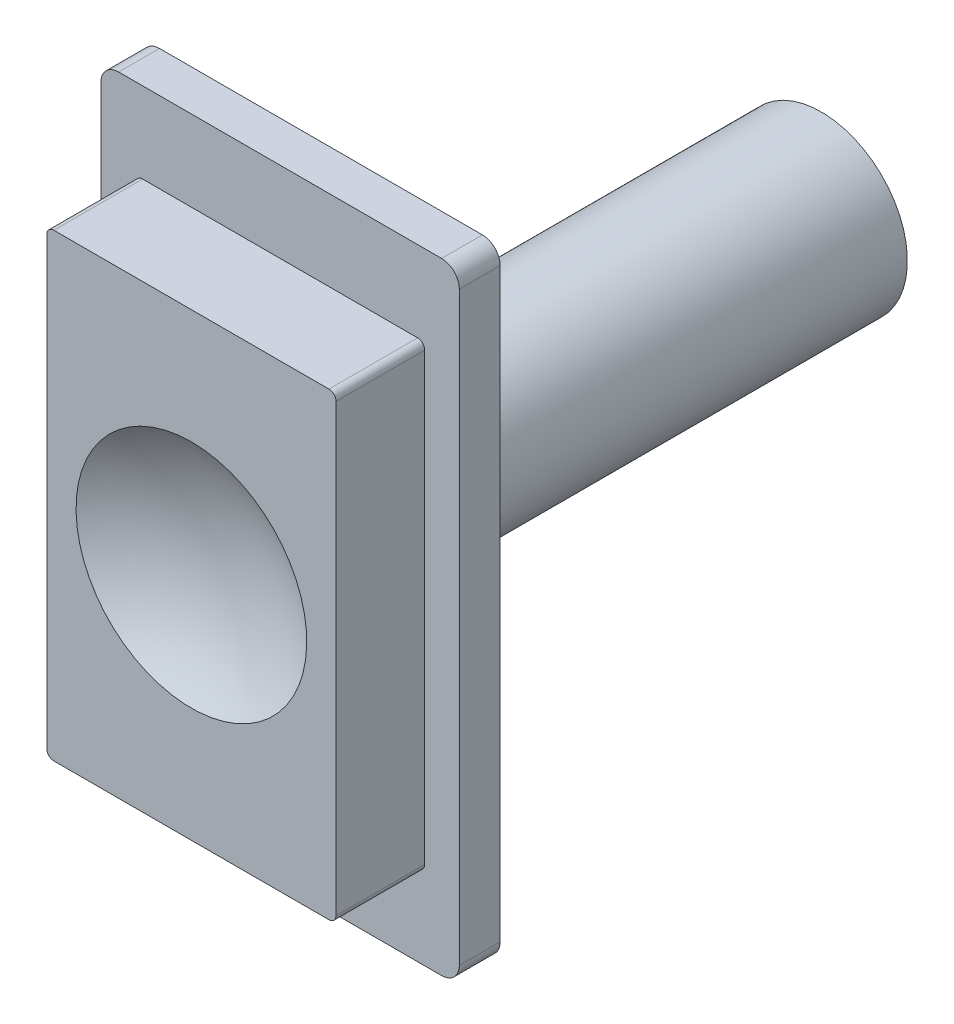
SolidWorks part; units mm, degrees
ref_plane "Front Plane" through (0, 0, 0) normal (1, 0, 0) x (0, 1, 0)
ref_plane "Top Plane" through (0, 0, 0) normal (0, 0, 1) x (0, 1, 0)
ref_plane "Right Plane" through (0, 0, 0) normal (0, 1, 0) x (-1, 0, 0)
sketch "Sketch1" plane through (0, 0, 0) normal (0, 0, 1) x (0, 1, 0)
  line L1 (-17.5, -10.1) -> (17.5, -10.1)
  line L2 (-17.5, -10.1) -> (-17.5, 10.1)
  line L3 (-17.5, 10.1) -> (17.5, 10.1)
  line L4 (17.5, -10.1) -> (17.5, 10.1)
  line L5 (-17.5, -10.1) -> (17.5, 10.1) construction
  line L6 (-17.5, 10.1) -> (17.5, -10.1) construction
  point P0 (0, 0)
  dimension "D1" = 20.2
  dimension "D2" = 35
extrude "Boss-Extrude1" add sketch "Sketch1" along normal blind 2.3
sketch "Sketch2" plane through (0, 0, 2.3) normal (0, 0, 1) x (1, 0, 0)
  line L1 (-8.15, -12.95) -> (8.15, -12.95)
  line L2 (-8.15, -12.95) -> (-8.15, 12.95)
  line L3 (-8.15, 12.95) -> (8.15, 12.95)
  line L4 (8.15, -12.95) -> (8.15, 12.95)
  line L5 (-8.15, -12.95) -> (8.15, 12.95) construction
  line L6 (-8.15, 12.95) -> (8.15, -12.95) construction
  point P0 (0, 0)
  dimension "D1" = 16.3
  dimension "D2" = 25.9
extrude "Boss-Extrude2" add sketch "Sketch2" along normal blind 5
sketch "Sketch4" plane through (0, 0, 0) normal (1, 0, 0) x (0, 1, 0)
  line L0 (0, 0) -> (0, 7.3) construction
  line L1 (-12.95, 7.3) -> (12.95, 7.3) construction
  line L2 (0, 7.3) -> (-6.5, 7.3)
  line L3 (0, 7.3) -> (0, 5.3)
  arc A0 (-6.5, 7.3) -> (0, 5.3) centre (0.0445, 17.007) ccw
revolve "Cut-Revolve1" cut sketch "Sketch4" angle 360 about L0
fillet "Fillet2" radius 1 4 edges at (-10.1, -17.5, 1.15) (-10.1, 17.5, 1.15) (10.1, 17.5, 1.15) (10.1, -17.5, 1.15)
fillet "Fillet3" radius 0.4 4 edges at (-8.15, 12.95, 4.8) (8.15, 12.95, 4.8) (8.15, -12.95, 4.8) (-8.15, -12.95, 4.8)
sketch "Sketch5" plane through (0, 0, 0) normal (0, 0, -1) x (1, 0, 0)
  circle A0 centre (0, 0) radius 4.85
extrude "Boss-Extrude3" add sketch "Sketch5" along normal blind 28.2
sketch "Sketch6" plane through (0, 0, -28.2) normal (0, 0, -1) x (1, 0, 0)
  line L0 (0, 0) -> (0, 3.15) construction
  line L1 (0, 0) -> (0, -3.15) construction
  line L3 (-0.5, 1.45) -> (0.5, 1.45)
  line L4 (-0.5, 1.45) -> (-0.5, 3.15)
  line L5 (-0.5, 3.15) -> (0.5, 3.15)
  line L6 (0.5, 1.45) -> (0.5, 3.15)
  line L7 (-0.5, 1.45) -> (0.5, 3.15) construction
  line L8 (-0.5, 3.15) -> (0.5, 1.45) construction
  line L9 (-0.5, -1.45) -> (0.5, -1.45)
  line L10 (-0.5, -1.45) -> (-0.5, -3.15)
  line L11 (-0.5, -3.15) -> (0.5, -3.15)
  line L12 (0.5, -1.45) -> (0.5, -3.15)
  line L13 (-0.5, -1.45) -> (0.5, -3.15) construction
  line L14 (-0.5, -3.15) -> (0.5, -1.45) construction
  circle A0 centre (0, 0) radius 2.3
  point P3 (0, 2.3)
  point P10 (0, -2.3)
  dimension "D1" = 1
  dimension "D2" = 1
extrude "Cut-Extrude3" cut sketch "Sketch6" against normal blind 16 contours A0 L6 L5 L4 | L12 A0 L6 L3 L4 L10 L9 | A0 L10 L11 L12 | L6 A0 L4 L3 | L10 A0 L12 L9
